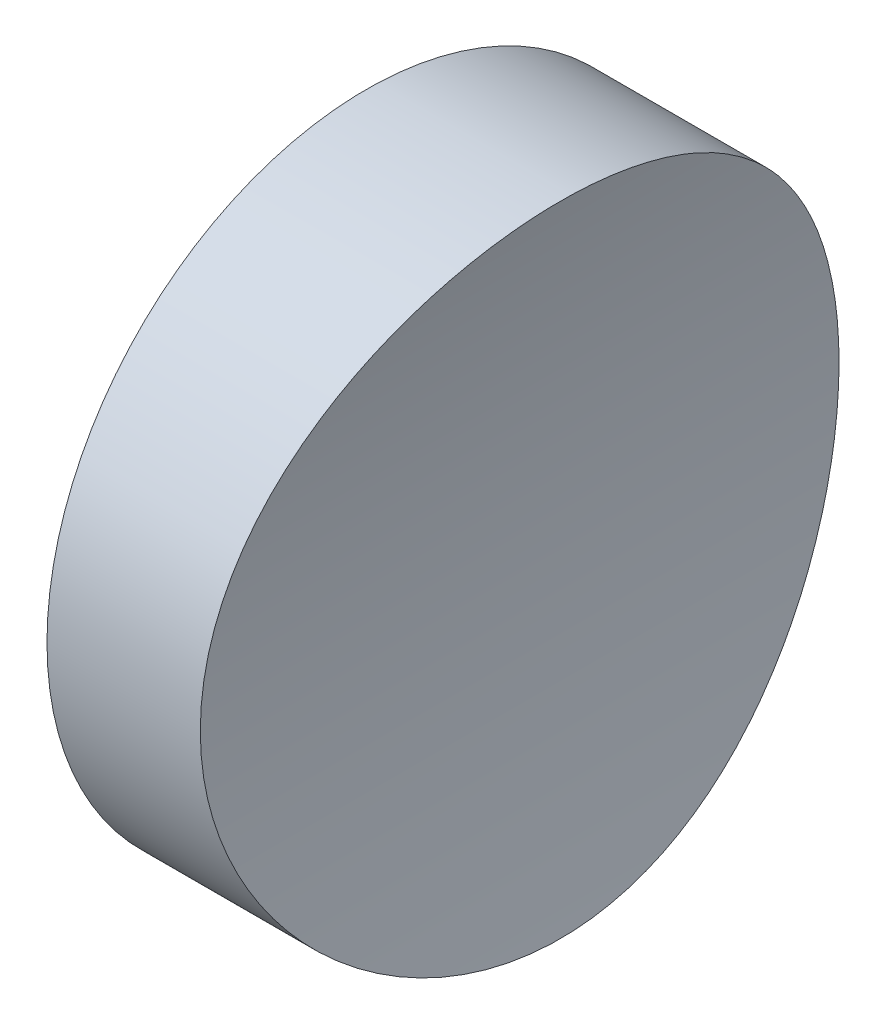
SolidWorks part; units mm, degrees
ref_plane "前视基准面" through (0, 0, 0) normal (0, 0, 1) x (1, 0, 0)
ref_plane "上视基准面" through (0, 0, 0) normal (0, 1, 0) x (1, 0, 0)
ref_plane "右视基准面" through (0, 0, 0) normal (1, 0, 0) x (0, 0, -1)
sketch "草图1" plane through (0, 0, 0) normal (1, 0, 0) x (0, 0, -1)
  circle A0 centre (0, 0) radius 6.25
  dimension "D1" = 12.5
extrude "凸台-拉伸1" add sketch "草图1" along normal blind 10
sketch "草图2" plane through (0, 0, 0) normal (0, 0, 1) x (1, 0, 0)
  line L0 (0, 0) -> (28, 0) construction
  line L1 (0, 0) -> (3, 0) construction
  circle A0 centre (28, 0) radius 25
  dimension "D1" = 50
  dimension "D2" = 3
extrude "切除-拉伸1" cut sketch "草图2" against normal through all both and the other way through all
